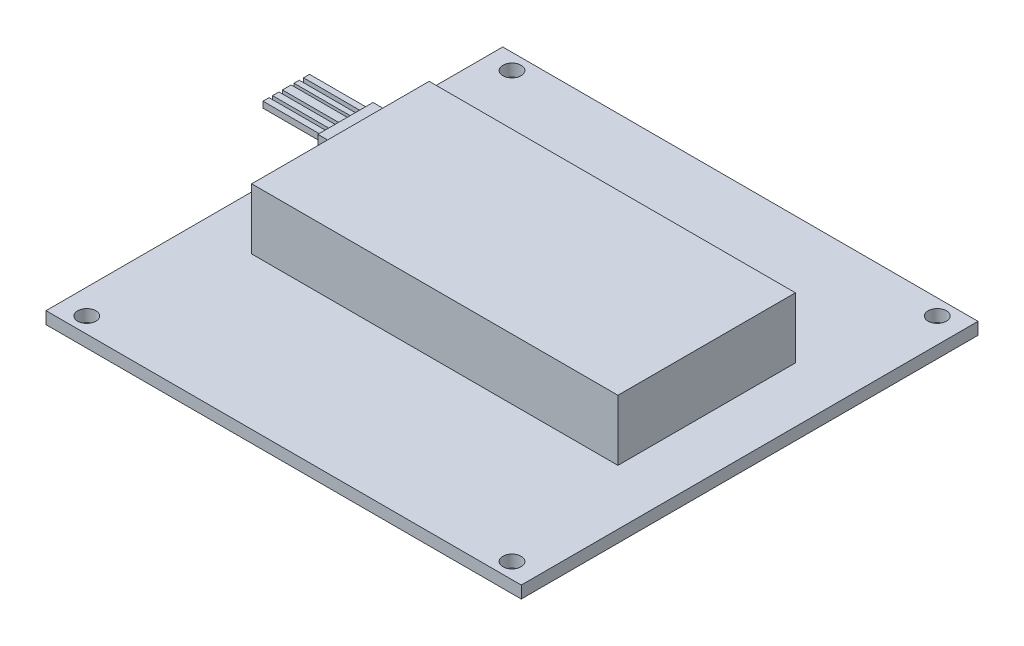
SolidWorks part; units mm, degrees
ref_plane "前视基准面" through (0, 0, 0) normal (0, 0, 1) x (1, 0, 0)
ref_plane "上视基准面" through (0, 0, 0) normal (0, 1, 0) x (1, 0, 0)
ref_plane "右视基准面" through (0, 0, 0) normal (1, 0, 0) x (0, 0, -1)
sketch "草图2" plane through (0, 0, 0) normal (0, 1, 0) x (1, 0, 0)
  line L1 (-39.116, 37.592) -> (39.116, 37.592)
  line L2 (-39.116, 37.592) -> (-39.116, -37.592)
  line L3 (-39.116, -37.592) -> (39.116, -37.592)
  line L4 (39.116, 37.592) -> (39.116, -37.592)
  line L5 (-39.116, 37.592) -> (39.116, -37.592) construction
  line L6 (-39.116, -37.592) -> (39.116, 37.592) construction
  line L7 (-35, -35) -> (35, -35) construction
  line L8 (-35, -35) -> (-35, 35) construction
  line L9 (-35, 35) -> (35, 35) construction
  line L10 (35, -35) -> (35, 35) construction
  line L11 (-35, -35) -> (35, 35) construction
  line L12 (-35, 35) -> (35, -35) construction
  circle A0 centre (35, -35) radius 1.5
  circle A1 centre (35, 35) radius 1.5
  circle A2 centre (-35, 35) radius 1.5
  circle A3 centre (-35, -35) radius 1.5
  point P0 (0, 0)
  point P5 (0, 0)
  dimension "D3" = 3
  dimension "D1" = 78.232
  dimension "D2" = 75.184
  dimension "D4" = 70
  dimension "D5" = 70
extrude "凸台-拉伸1" add sketch "草图2" along normal blind 2
sketch "草图3" plane through (0, 2, 0) normal (0, 1, 0) x (1, 0, 0)
  text T0 "控制板" font "汉仪长仿宋体" height 7
sketch "草图4" plane through (0, 2, 0) normal (0, 1, 0) x (1, 0, 0)
  line L1 (-30.272, 16.6347) -> (30.0179, 16.6347)
  line L2 (-30.272, 16.6347) -> (-30.272, -12.5798)
  line L3 (-30.272, -12.5798) -> (30.0179, -12.5798)
  line L4 (30.0179, 16.6347) -> (30.0179, -12.5798)
extrude "凸台-拉伸2" add sketch "草图4" along normal blind 10
sketch "草图5" plane through (-30.272, 0, 0) normal (-1, 0, 0) x (0, 0, 1)
  line L1 (-11.3945, 9.6071) -> (-2.3079, 9.6071)
  line L2 (-11.3945, 9.6071) -> (-11.3945, 7.1898)
  line L3 (-11.3945, 7.1898) -> (-2.3079, 7.1898)
  line L4 (-2.3079, 9.6071) -> (-2.3079, 7.1898)
extrude "凸台-拉伸3" add sketch "草图5" along normal blind 4
sketch "草图6" plane through (-34.272, 0, 0) normal (-1, 0, 0) x (0, 0, 1)
  line L1 (-9.2541, 8.8477) -> (-8.3942, 8.8477)
  line L2 (-9.2541, 8.8477) -> (-9.2541, 7.7967)
  line L3 (-9.2541, 7.7967) -> (-8.3942, 7.7967)
  line L4 (-8.3942, 8.8477) -> (-8.3942, 7.7967)
  line L5 (-7.9165, 8.8477) -> (-6.4834, 8.8477)
  line L6 (-7.9165, 8.8477) -> (-7.9165, 7.8445)
  line L7 (-7.9165, 7.8445) -> (-6.4834, 7.8445)
  line L8 (-6.4834, 8.8477) -> (-6.4834, 7.8445)
  line L9 (-5.9102, 8.8477) -> (-4.8592, 8.8477)
  line L10 (-5.9102, 8.8477) -> (-5.9102, 7.8445)
  line L11 (-5.9102, 7.8445) -> (-4.8592, 7.8445)
  line L12 (-4.8592, 8.8477) -> (-4.8592, 7.8445)
  line L13 (-4.286, 8.8477) -> (-3.2828, 8.8477)
  line L14 (-4.286, 8.8477) -> (-4.286, 7.8445)
  line L15 (-4.286, 7.8445) -> (-3.2828, 7.8445)
  line L16 (-3.2828, 8.8477) -> (-3.2828, 7.8445)
  line L17 (-10.9383, 8.8477) -> (-9.955, 8.8477)
  line L18 (-10.9383, 8.8477) -> (-10.9383, 7.7967)
  line L19 (-10.9383, 7.7967) -> (-9.955, 7.7967)
  line L20 (-9.955, 8.8477) -> (-9.955, 7.7967)
extrude "凸台-拉伸4" add sketch "草图6" along normal blind 10
